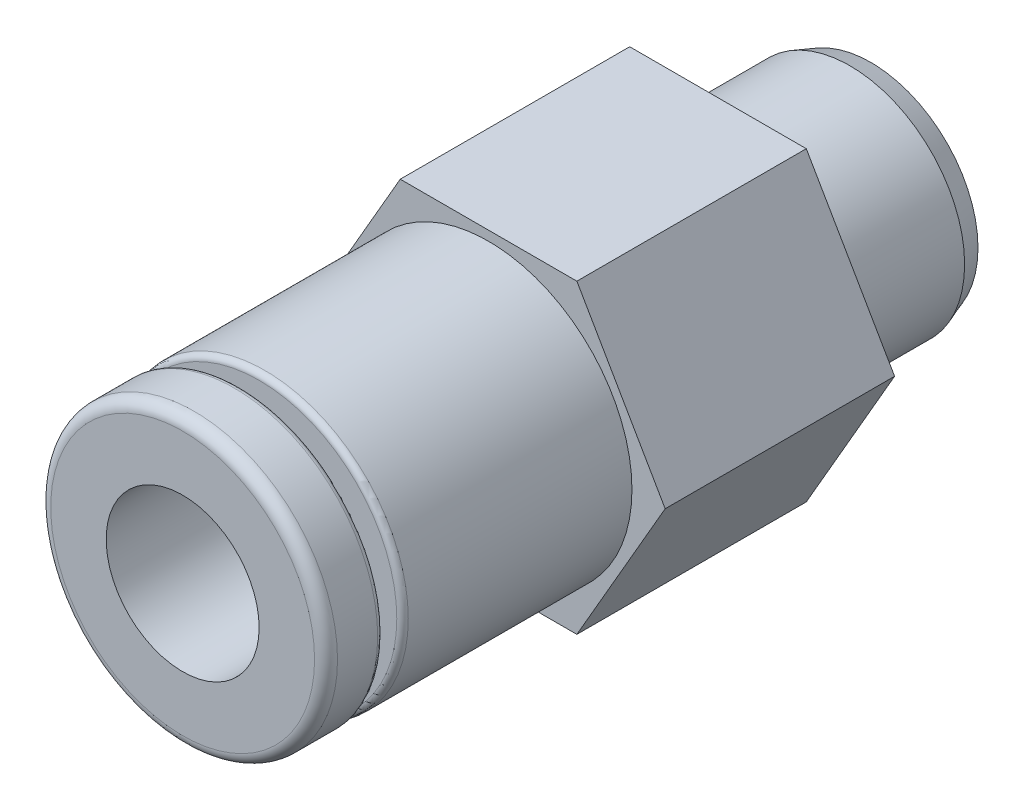
SolidWorks part; units mm, degrees
material "AISI 1020"
ref_plane "Plan de face" through (0, 0, 0) normal (0, 0, 1) x (1, 0, 0)
ref_plane "Plan de dessus" through (0, 0, 0) normal (0, 1, 0) x (1, 0, 0)
ref_plane "Plan de droite" through (0, 0, 0) normal (1, 0, 0) x (0, 0, -1)
sketch "Esquisse1" plane through (0, 0, 0) normal (0, 0, 1) x (1, 0, 0)
  circle A0 centre (0, 0) radius 3
  circle A1 centre (0, 0) radius 1.25
  dimension "D1" = 6
  dimension "D2" = 2.5
extrude "Boss.-Extru.1" add sketch "Esquisse1" along normal blind 4
cosmetic thread "Représentation de filetage1" parameters "D1"=0, "D2"=0
chamfer "Chanfrein1" distance 0.2 angle 70 1 edges at (3, 0, 0)
sketch "Esquisse2" plane through (0, 0, 4) normal (0, 0, 1) x (1, 0, 0)
  line L1 (2.3094, -4) -> (4.6188, 0)
  line L2 (4.6188, 0) -> (2.3094, 4)
  line L3 (2.3094, 4) -> (-2.3094, 4)
  line L4 (-2.3094, 4) -> (-4.6188, 0)
  line L5 (-4.6188, 0) -> (-2.3094, -4)
  line L6 (-2.3094, -4) -> (2.3094, -4)
  circle A0 centre (0, 0) radius 4 construction
  circle A1 centre (0, 0) radius 2
  dimension "D1" = 8
  dimension "D2" = 4
extrude "Boss.-Extru.2" add sketch "Esquisse2" along normal blind 6
sketch "Esquisse3" plane through (0, 0, 10) normal (0, 0, 1) x (1, 0, 0)
  circle A0 centre (0, 0) radius 2
  circle A1 centre (0, 0) radius 3.75
  dimension "D1" = 7.5
extrude "Boss.-Extru.3" add sketch "Esquisse3" along normal blind 8
fillet "Congé3" radius 0.3 1 edges at (3, 0, 4)
ref_axis "Axe1" through (0, 0, 52.2414) along (0, 0, -1)
sketch "Esquisse4" plane through (0, 0, 0) normal (0, 1, 0) x (1, 0, 0)
  line L0 (3.75, -18) -> (3.75, -10) construction
  line L1 (3.75, -16.5) -> (2.25, -16.5)
  line L2 (3.75, -16.5) -> (3.75, -16)
  line L3 (3.75, -16) -> (2.25, -16)
  line L4 (2.25, -16.5) -> (2.25, -16)
  line L5 (-3.75, -18) -> (3.75, -18) construction
  dimension "D1" = 1.5
  dimension "D2" = 0.5
  dimension "D3" = 1.5
revolve "Enlèvement de matière-Révolution1" cut sketch "Esquisse4" angle 360 about axis through (0, 0, 52.2414) along (0, 0, -1)
fillet "Congé4" radius 0.3 1 edges at (3.75, 0, 18)
fillet "Congé5" radius 0.15 2 edges at (3.75, 0, 16.5) (3.75, 0, 16)
